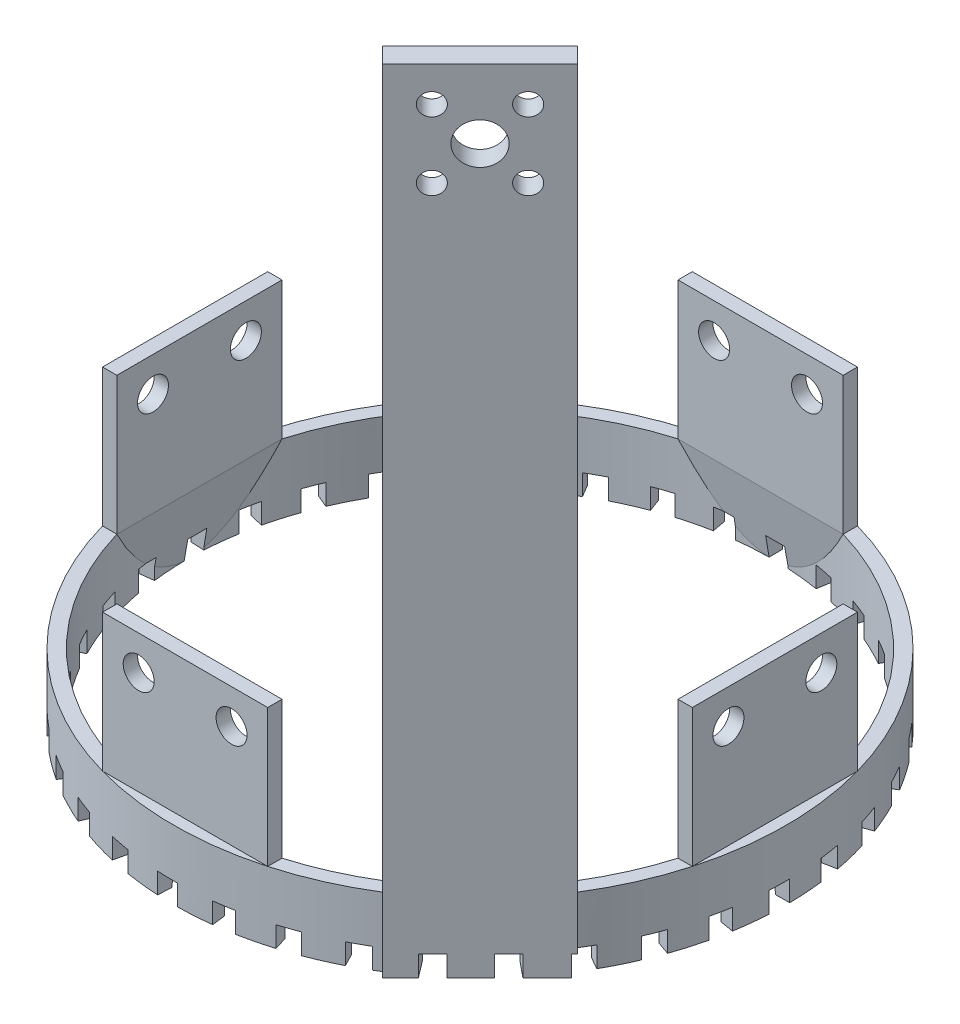
SolidWorks part; units mm, degrees
ref_plane "前视基准面" through (0, 0, 0) normal (0, 0, 1) x (1, 0, 0)
ref_plane "上视基准面" through (0, 0, 0) normal (0, 1, 0) x (1, 0, 0)
ref_plane "右视基准面" through (0, 0, 0) normal (1, 0, 0) x (0, 0, -1)
sketch "草图1" plane through (0, 0, 0) normal (0, 1, 0) x (1, 0, 0)
  circle A0 centre (0, 0) radius 44.5
  circle A5 centre (0, 0) radius 42.5
  dimension "D1" = 89
  dimension "D2" = 85
extrude "凸台-拉伸1" add sketch "草图1" along normal blind 10
sketch "草图6" plane through (0, 10, 0) normal (0, 1, 0) x (1, 0, 0)
  line L0 (0, 0) -> (0, 44.5) construction
  line L2 (12, 42.8515) -> (12, 40.7707)
  line L3 (-12, 42.8515) -> (-12, 40.7707)
  line L13 (-12, 42.8515) -> (12, 42.8515)
  line L14 (-12, 40.7707) -> (12, 40.7707)
  line L15 (40.7707, 12) -> (40.7707, -12)
  line L16 (42.8515, 12) -> (40.7707, 12)
  line L17 (42.8515, 12) -> (42.8515, -12)
  line L18 (42.8515, -12) -> (40.7707, -12)
  line L19 (12, -40.7707) -> (-12, -40.7707)
  line L20 (12, -42.8515) -> (12, -40.7707)
  line L21 (12, -42.8515) -> (-12, -42.8515)
  line L22 (-12, -42.8515) -> (-12, -40.7707)
  line L23 (-40.7707, -12) -> (-40.7707, 12)
  line L24 (-42.8515, -12) -> (-40.7707, -12)
  line L25 (-42.8515, -12) -> (-42.8515, 12)
  line L26 (-42.8515, 12) -> (-40.7707, 12)
  circle A0 centre (0, 0) radius 44.5 construction
  circle A1 centre (0, 0) radius 42.5 construction
  point P27 (0, 0)
  point P28 (0, 0)
  dimension "D1" = 4
extrude "凸台-拉伸3" add sketch "草图6" along normal blind 20
sketch "草图7" plane through (-44.5, 0, 0) normal (-1, 0, 0) x (0, 0, 1)
  line L0 (0, 10) -> (0, 0) construction
  line L3 (-44.5, 0) -> (44.5, 0) construction
  circle A0 centre (-6.75, 25) radius 2.25
  circle A1 centre (6.75, 25) radius 2.25
  dimension "D1" = 25
  dimension "D2" = 6.75
extrude "切除-拉伸1" cut sketch "草图7" against normal through all
sketch "草图8" plane through (0, 0, -44.5) normal (0, 0, -1) x (-1, 0, 0)
  line L0 (0, 0) -> (0, 10) construction
  line L3 (-44.5, 0) -> (44.5, 0) construction
  circle A0 centre (-6.75, 25) radius 2.25
  circle A1 centre (6.75, 25) radius 2.25
  dimension "D1" = 6.75
  dimension "D2" = 25
extrude "切除-拉伸2" cut sketch "草图8" against normal through all
sketch "草图9" plane through (12, 0, 0) normal (1, 0, 0) x (0, 0, -1)
  line L1 (-42.8515, 0) -> (-42.8515, 10)
  line L2 (-42.8515, 10) -> (-40.7707, 10)
  line L3 (0, 30) -> (0, 0) construction
  line L4 (-12, 30) -> (12, 30) construction
  line L5 (42.8515, 10) -> (40.7707, 10)
  line L6 (42.8515, 0) -> (42.8515, 10)
  line L8 (-40.7707, 10) -> (-42.5, 0)
  line L9 (-42.5, 0) -> (-42.8515, 0)
  line L10 (40.7707, 10) -> (42.5, 0)
  line L11 (42.5, 0) -> (42.8515, 0)
extrude "凸台-拉伸4" add sketch "草图9" against normal blind 24
sketch "草图10" plane through (0, 0, 12) normal (0, 0, 1) x (1, 0, 0)
  line L1 (-44.5, 0) -> (44.5, 0) construction
  line L2 (-42.8515, 0) -> (-42.8515, 10)
  line L3 (-42.8515, 10) -> (-40.7707, 10)
  line L4 (0, 30) -> (0, 0) construction
  line L5 (-12, 30) -> (12, 30) construction
  line L6 (42.8515, 10) -> (40.7707, 10)
  line L7 (42.8515, 0) -> (42.8515, 10)
  line L9 (-40.7707, 10) -> (-42.5, 0)
  line L10 (-42.5, 0) -> (-42.8515, 0)
  line L11 (40.7707, 10) -> (42.5, 0)
  line L12 (42.5, 0) -> (42.8515, 0)
extrude "凸台-拉伸5" add sketch "草图10" against normal blind 24
sketch "草图12" plane through (0, 10, 0) normal (0, 1, 0) x (1, 0, 0)
  line L0 (0, 0) -> (31.4663, -31.4663) construction
  line L1 (36.2794, -22.1372) -> (38.5373, -24.3952)
  line L2 (22.1064, -36.2485) -> (24.3952, -38.5373)
  line L4 (22.1064, -36.2485) -> (36.2794, -22.1372)
  line L6 (38.5373, -24.3952) -> (24.3952, -38.5373)
  arc A0 (12, -42.8515) -> (42.8515, -12) centre (0, 0) ccw construction
  dimension "D1" = 10
extrude "凸台-拉伸6" add sketch "草图12" along normal blind 105 and the other way blind 10
sketch "草图13" plane through (-7.0711, 0, 7.0711) normal (-0.7071, 0, 0.7071) x (0.7071, 0, 0.7071)
  line L1 (43.3618, 10) -> (41.2632, 10)
  line L3 (43.3618, 10) -> (43.3618, 0)
  line L5 (41.2632, 10) -> (42.5, 0)
  line L6 (-44.5, 0) -> (43.3618, 0) construction
  line L7 (43.3618, 0) -> (42.5, 0)
extrude "凸台-拉伸11" add sketch "草图13" against normal blind 20
sketch "草图14" plane through (30.6615, 0, 30.6615) normal (0.7071, 0, 0.7071) x (0.7071, 0, -0.7071)
  line L0 (0, 110) -> (0, 10) construction
  line L2 (-10, 10) -> (10, 10) construction
  line L3 (-4.9497, 109.9497) -> (4.9497, 100.0503) construction
  line L5 (-10, 115) -> (10, 115) construction
  circle A4 centre (4.9497, 109.9497) radius 1.6
  circle A5 centre (-4.9497, 100.0503) radius 1.6
  circle A6 centre (-4.9497, 109.9497) radius 1.6
  circle A7 centre (4.9497, 100.0503) radius 1.6
  circle A8 centre (0, 105) radius 3
  point P6 (0, 110)
  dimension "D1" = 9.8995
  dimension "D3" = 10
  dimension "D2" = 9.8995
extrude "切除-拉伸4" cut sketch "草图14" against normal through all and the other way through all
sketch "草图15" plane through (0, 0, 0) normal (0, -1, 0) x (1, 0, 0)
  line L0 (-13.5043, 38.4692) -> (-15.1072, 43.0351)
  line L1 (-16.015, 37.4936) -> (-17.8936, 41.9532)
  line L2 (-9.261, 39.705) -> (-10.3366, 44.423)
  line L3 (-6.6191, 40.2298) -> (-7.4047, 45.0047)
  line L4 (-2.2256, 40.7099) -> (-2.4656, 45.5431)
  line L5 (0.4673, 40.768) -> (0.5228, 45.6068)
  line L6 (4.8774, 40.4779) -> (5.4803, 45.2793)
  line L7 (7.5395, 40.0675) -> (8.4344, 44.8231)
  line L8 (11.8322, 39.016) -> (13.2597, 43.6398)
  line L9 (14.3826, 38.1496) -> (16.0897, 42.6775)
  line L10 (18.4275, 36.3686) -> (20.6362, 40.6743)
  line L11 (20.7887, 35.0725) -> (23.2561, 39.2352)
  line L12 (24.4629, 32.6162) -> (27.3857, 36.4729)
  line L13 (26.5632, 30.9297) -> (29.7159, 34.6008)
  line L14 (29.755, 27.8727) -> (33.3031, 31.1633)
  line L15 (31.5305, 25.8472) -> (35.2728, 28.915)
  line L16 (34.143, 22.2824) -> (38.2086, 24.9068)
  line L17 (35.5398, 19.9793) -> (39.758, 22.3506)
  line L18 (37.4936, 16.015) -> (41.9532, 17.8936)
  line L19 (38.4692, 13.5043) -> (43.0351, 15.1072)
  line L20 (39.705, 9.261) -> (44.423, 10.3366)
  line L21 (40.2298, 6.6191) -> (45.0047, 7.4047)
  line L22 (40.7099, 2.2256) -> (45.5431, 2.4656)
  line L23 (40.768, -0.4673) -> (45.6068, -0.5228)
  line L24 (40.4779, -4.8774) -> (45.2793, -5.4803)
  line L25 (40.0675, -7.5395) -> (44.8231, -8.4344)
  line L26 (39.016, -11.8322) -> (43.6398, -13.2597)
  line L27 (38.1496, -14.3826) -> (42.6775, -16.0897)
  line L28 (36.3686, -18.4275) -> (40.6743, -20.6362)
  line L29 (35.0725, -20.7887) -> (39.2352, -23.2561)
  line L30 (32.6162, -24.4629) -> (36.4729, -27.3857)
  line L31 (30.9297, -26.5632) -> (34.6008, -29.7159)
  line L32 (27.8727, -29.755) -> (31.1633, -33.3031)
  line L33 (25.8472, -31.5305) -> (28.915, -35.2728)
  line L34 (22.2824, -34.143) -> (24.9068, -38.2086)
  line L35 (19.9793, -35.5398) -> (22.3506, -39.758)
  line L36 (16.015, -37.4936) -> (17.8936, -41.9532)
  line L37 (13.5043, -38.4692) -> (15.1072, -43.0351)
  line L38 (9.261, -39.705) -> (10.3366, -44.423)
  line L39 (6.6191, -40.2298) -> (7.4047, -45.0047)
  line L40 (2.2256, -40.7099) -> (2.4656, -45.5431)
  line L41 (-0.4673, -40.768) -> (-0.5228, -45.6068)
  line L42 (-4.8774, -40.4779) -> (-5.4803, -45.2793)
  line L43 (-7.5395, -40.0675) -> (-8.4344, -44.8231)
  line L44 (-11.8322, -39.016) -> (-13.2597, -43.6398)
  line L45 (-14.3826, -38.1496) -> (-16.0897, -42.6775)
  line L46 (-18.4275, -36.3686) -> (-20.6362, -40.6743)
  line L47 (-20.7887, -35.0725) -> (-23.2561, -39.2352)
  line L48 (-24.4629, -32.6162) -> (-27.3857, -36.4729)
  line L49 (-26.5632, -30.9297) -> (-29.7159, -34.6008)
  line L50 (-29.755, -27.8727) -> (-33.3031, -31.1633)
  line L51 (-31.5305, -25.8472) -> (-35.2728, -28.915)
  line L52 (-34.143, -22.2824) -> (-38.2086, -24.9068)
  line L53 (-35.5398, -19.9793) -> (-39.758, -22.3506)
  line L54 (-37.4936, -16.015) -> (-41.9532, -17.8936)
  line L55 (-38.4692, -13.5043) -> (-43.0351, -15.1072)
  line L56 (-39.705, -9.261) -> (-44.423, -10.3366)
  line L57 (-40.2298, -6.6191) -> (-45.0047, -7.4047)
  line L58 (-40.7099, -2.2256) -> (-45.5431, -2.4656)
  line L59 (-40.768, 0.4673) -> (-45.6068, 0.5228)
  line L60 (-40.4779, 4.8774) -> (-45.2793, 5.4803)
  line L61 (-40.0675, 7.5395) -> (-44.8231, 8.4344)
  line L62 (-39.016, 11.8322) -> (-43.6398, 13.2597)
  line L63 (-38.1496, 14.3826) -> (-42.6775, 16.0897)
  line L64 (-36.3686, 18.4275) -> (-40.6743, 20.6362)
  line L65 (-35.0725, 20.7887) -> (-39.2352, 23.2561)
  line L66 (-32.6162, 24.4629) -> (-36.4729, 27.3857)
  line L67 (-30.9297, 26.5632) -> (-34.6008, 29.7159)
  line L68 (-27.8727, 29.755) -> (-31.1633, 33.3031)
  line L69 (-25.8472, 31.5305) -> (-28.915, 35.2728)
  line L70 (-22.2824, 34.143) -> (-24.9068, 38.2086)
  line L71 (-19.9793, 35.5398) -> (-22.3506, 39.758)
  arc A0 (-13.5043, 38.4692) -> (-16.015, 37.4936) centre (0, 0) ccw
  arc A1 (-15.1072, 43.0351) -> (-17.8936, 41.9532) centre (0, 0) ccw
  arc A2 (-7.4047, 45.0047) -> (-10.3366, 44.423) centre (0, 0) ccw
  arc A3 (-6.6191, 40.2298) -> (-9.261, 39.705) centre (0, 0) ccw
  arc A4 (0.5228, 45.6068) -> (-2.4656, 45.5431) centre (0, 0) ccw
  arc A5 (0.4673, 40.768) -> (-2.2256, 40.7099) centre (0, 0) ccw
  arc A6 (8.4344, 44.8231) -> (5.4803, 45.2793) centre (0, 0) ccw
  arc A7 (7.5395, 40.0675) -> (4.8774, 40.4779) centre (0, 0) ccw
  arc A8 (16.0897, 42.6775) -> (13.2597, 43.6398) centre (0, 0) ccw
  arc A9 (14.3826, 38.1496) -> (11.8322, 39.016) centre (0, 0) ccw
  arc A10 (23.2561, 39.2352) -> (20.6362, 40.6743) centre (0, 0) ccw
  arc A11 (20.7887, 35.0725) -> (18.4275, 36.3686) centre (0, 0) ccw
  arc A12 (29.7159, 34.6008) -> (27.3857, 36.4729) centre (0, 0) ccw
  arc A13 (26.5632, 30.9297) -> (24.4629, 32.6162) centre (0, 0) ccw
  arc A14 (35.2728, 28.915) -> (33.3031, 31.1633) centre (0, 0) ccw
  arc A15 (31.5305, 25.8472) -> (29.755, 27.8727) centre (0, 0) ccw
  arc A16 (39.758, 22.3506) -> (38.2086, 24.9068) centre (0, 0) ccw
  arc A17 (35.5398, 19.9793) -> (34.143, 22.2824) centre (0, 0) ccw
  arc A18 (43.0351, 15.1072) -> (41.9532, 17.8936) centre (0, 0) ccw
  arc A19 (38.4692, 13.5043) -> (37.4936, 16.015) centre (0, 0) ccw
  arc A20 (45.0047, 7.4047) -> (44.423, 10.3366) centre (0, 0) ccw
  arc A21 (40.2298, 6.6191) -> (39.705, 9.261) centre (0, 0) ccw
  arc A22 (45.6068, -0.5228) -> (45.5431, 2.4656) centre (0, 0) ccw
  arc A23 (40.768, -0.4673) -> (40.7099, 2.2256) centre (0, 0) ccw
  arc A24 (44.8231, -8.4344) -> (45.2793, -5.4803) centre (0, 0) ccw
  arc A25 (40.0675, -7.5395) -> (40.4779, -4.8774) centre (0, 0) ccw
  arc A26 (42.6775, -16.0897) -> (43.6398, -13.2597) centre (0, 0) ccw
  arc A27 (38.1496, -14.3826) -> (39.016, -11.8322) centre (0, 0) ccw
  arc A28 (39.2352, -23.2561) -> (40.6743, -20.6362) centre (0, 0) ccw
  arc A29 (35.0725, -20.7887) -> (36.3686, -18.4275) centre (0, 0) ccw
  arc A30 (34.6008, -29.7159) -> (36.4729, -27.3857) centre (0, 0) ccw
  arc A31 (30.9297, -26.5632) -> (32.6162, -24.4629) centre (0, 0) ccw
  arc A32 (28.915, -35.2728) -> (31.1633, -33.3031) centre (0, 0) ccw
  arc A33 (25.8472, -31.5305) -> (27.8727, -29.755) centre (0, 0) ccw
  arc A34 (22.3506, -39.758) -> (24.9068, -38.2086) centre (0, 0) ccw
  arc A35 (19.9793, -35.5398) -> (22.2824, -34.143) centre (0, 0) ccw
  arc A36 (15.1072, -43.0351) -> (17.8936, -41.9532) centre (0, 0) ccw
  arc A37 (13.5043, -38.4692) -> (16.015, -37.4936) centre (0, 0) ccw
  arc A38 (7.4047, -45.0047) -> (10.3366, -44.423) centre (0, 0) ccw
  arc A39 (6.6191, -40.2298) -> (9.261, -39.705) centre (0, 0) ccw
  arc A40 (-0.5228, -45.6068) -> (2.4656, -45.5431) centre (0, 0) ccw
  arc A41 (-0.4673, -40.768) -> (2.2256, -40.7099) centre (0, 0) ccw
  arc A42 (-8.4344, -44.8231) -> (-5.4803, -45.2793) centre (0, 0) ccw
  arc A43 (-7.5395, -40.0675) -> (-4.8774, -40.4779) centre (0, 0) ccw
  arc A44 (-16.0897, -42.6775) -> (-13.2597, -43.6398) centre (0, 0) ccw
  arc A45 (-14.3826, -38.1496) -> (-11.8322, -39.016) centre (0, 0) ccw
  arc A46 (-23.2561, -39.2352) -> (-20.6362, -40.6743) centre (0, 0) ccw
  arc A47 (-20.7887, -35.0725) -> (-18.4275, -36.3686) centre (0, 0) ccw
  arc A48 (-29.7159, -34.6008) -> (-27.3857, -36.4729) centre (0, 0) ccw
  arc A49 (-26.5632, -30.9297) -> (-24.4629, -32.6162) centre (0, 0) ccw
  arc A50 (-35.2728, -28.915) -> (-33.3031, -31.1633) centre (0, 0) ccw
  arc A51 (-31.5305, -25.8472) -> (-29.755, -27.8727) centre (0, 0) ccw
  arc A52 (-39.758, -22.3506) -> (-38.2086, -24.9068) centre (0, 0) ccw
  arc A53 (-35.5398, -19.9793) -> (-34.143, -22.2824) centre (0, 0) ccw
  arc A54 (-43.0351, -15.1072) -> (-41.9532, -17.8936) centre (0, 0) ccw
  arc A55 (-38.4692, -13.5043) -> (-37.4936, -16.015) centre (0, 0) ccw
  arc A56 (-45.0047, -7.4047) -> (-44.423, -10.3366) centre (0, 0) ccw
  arc A57 (-40.2298, -6.6191) -> (-39.705, -9.261) centre (0, 0) ccw
  arc A58 (-45.6068, 0.5228) -> (-45.5431, -2.4656) centre (0, 0) ccw
  arc A59 (-40.768, 0.4673) -> (-40.7099, -2.2256) centre (0, 0) ccw
  arc A60 (-44.8231, 8.4344) -> (-45.2793, 5.4803) centre (0, 0) ccw
  arc A61 (-40.0675, 7.5395) -> (-40.4779, 4.8774) centre (0, 0) ccw
  arc A62 (-42.6775, 16.0897) -> (-43.6398, 13.2597) centre (0, 0) ccw
  arc A63 (-38.1496, 14.3826) -> (-39.016, 11.8322) centre (0, 0) ccw
  arc A64 (-39.2352, 23.2561) -> (-40.6743, 20.6362) centre (0, 0) ccw
  arc A65 (-35.0725, 20.7887) -> (-36.3686, 18.4275) centre (0, 0) ccw
  arc A66 (-34.6008, 29.7159) -> (-36.4729, 27.3857) centre (0, 0) ccw
  arc A67 (-30.9297, 26.5632) -> (-32.6162, 24.4629) centre (0, 0) ccw
  arc A68 (-28.915, 35.2728) -> (-31.1633, 33.3031) centre (0, 0) ccw
  arc A69 (-25.8472, 31.5305) -> (-27.8727, 29.755) centre (0, 0) ccw
  arc A70 (-22.3506, 39.758) -> (-24.9068, 38.2086) centre (0, 0) ccw
  arc A71 (-19.9793, 35.5398) -> (-22.2824, 34.143) centre (0, 0) ccw
  point P149 (0, 0)
  dimension "D1" = 3.5
  dimension "D2" = 36
extrude "切除-拉伸6" cut sketch "草图15" against normal blind 3
